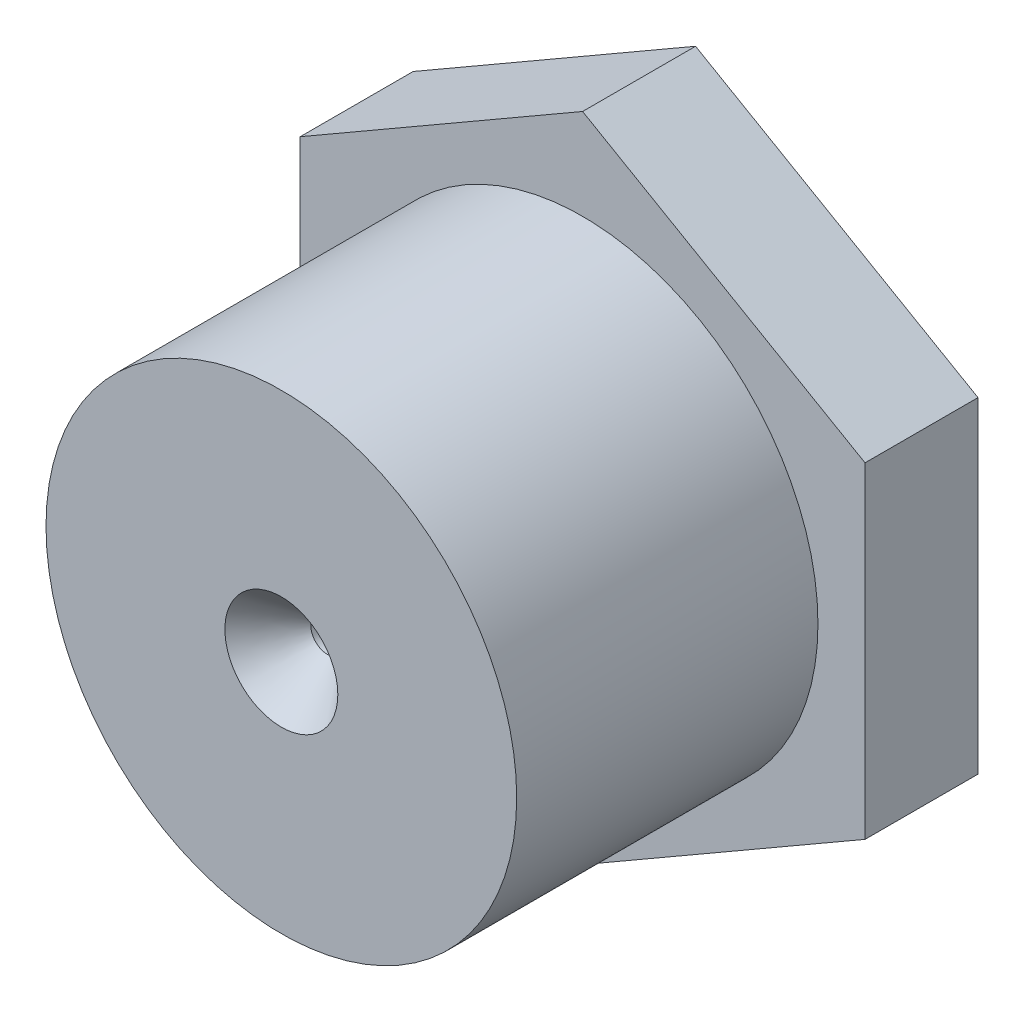
SolidWorks part; units mm, degrees
material "Lega 1060"
ref_plane "Piano frontale" through (0, 0, 0) normal (0, 0, 1) x (1, 0, 0)
ref_plane "Piano superiore" through (0, 0, 0) normal (0, 1, 0) x (1, 0, 0)
ref_plane "Piano destro" through (0, 0, 0) normal (1, 0, 0) x (0, 0, -1)
sketch "Schizzo1" plane through (0, 0, 0) normal (0, 0, 1) x (1, 0, 0)
  line L1 (0, 17.3205) -> (-15, 8.6603)
  line L2 (-15, 8.6603) -> (-15, -8.6603)
  line L3 (-15, -8.6603) -> (0, -17.3205)
  line L4 (0, -17.3205) -> (15, -8.6603)
  line L5 (15, -8.6603) -> (15, 8.6603)
  line L6 (15, 8.6603) -> (0, 17.3205)
  circle A0 centre (0, 0) radius 15 construction
  dimension "D1" = 30
extrude "Estrusione-Estrusione1" add sketch "Schizzo1" along normal blind 6
sketch "Schizzo2" plane through (0, 0, 6) normal (0, 0, 1) x (1, 0, 0)
  circle A0 centre (0, 0) radius 12.5
  dimension "D1" = 25
extrude "Estrusione-Estrusione2" add sketch "Schizzo2" along normal blind 16
cosmetic thread "Filettatura cosmetica1" parameters "D1"=10, "D2"=22
cosmetic thread "Filettatura cosmetica2" parameters "D1"=15, "D2"=20.704
hole_wizard "Foro1" positions "Schizzo6" profile "Schizzo5" legacy end condition through all
sketch "Schizzo6" plane through (0, 0, 22) normal (0, 0, 1) x (1, 0, 0)
  point P0 (0, 0)
sketch "Schizzo5" plane through (0, 0, 22) normal (1, 0, 0) x (0, -1, 0)
  line L0 (0, 0) -> (0, 22)
  line L1 (0, 22) -> (0.875, 22)
  line L2 (0.875, 22) -> (0.875, 2.4445)
  line L3 (0.875, 2.4445) -> (3, 0)
  line L4 (3, 0) -> (0, 0)
  line L5 (0, -6.4453) -> (0, 115.525) construction
  line L6 (-0.875, 2.4445) -> (-3, 0) construction
  dimension "Diameter" = 1.75
  dimension "Depth" = 22
  dimension "C-Sink Angle" = 82
  dimension "C-Sink Diameter" = 6
sketch "Schizzo7" plane through (0, 0, 0) normal (0, 1, 0) x (1, 0, 0)
  line L0 (-1.5, 0) -> (0, -1.5)
  line L1 (0, 0) -> (-15, 0) construction
  line L2 (0, -6) -> (0, 0) construction
  line L3 (0, -1.5) -> (0, 0)
  line L4 (15, 0) -> (0, 0) construction
  line L5 (0, 0) -> (-1.5, 0)
  dimension "D1" = 45
  dimension "D2" = 1.5
revolve "Taglia-Rivoluzione1" cut sketch "Schizzo7" angle 360 about L3
